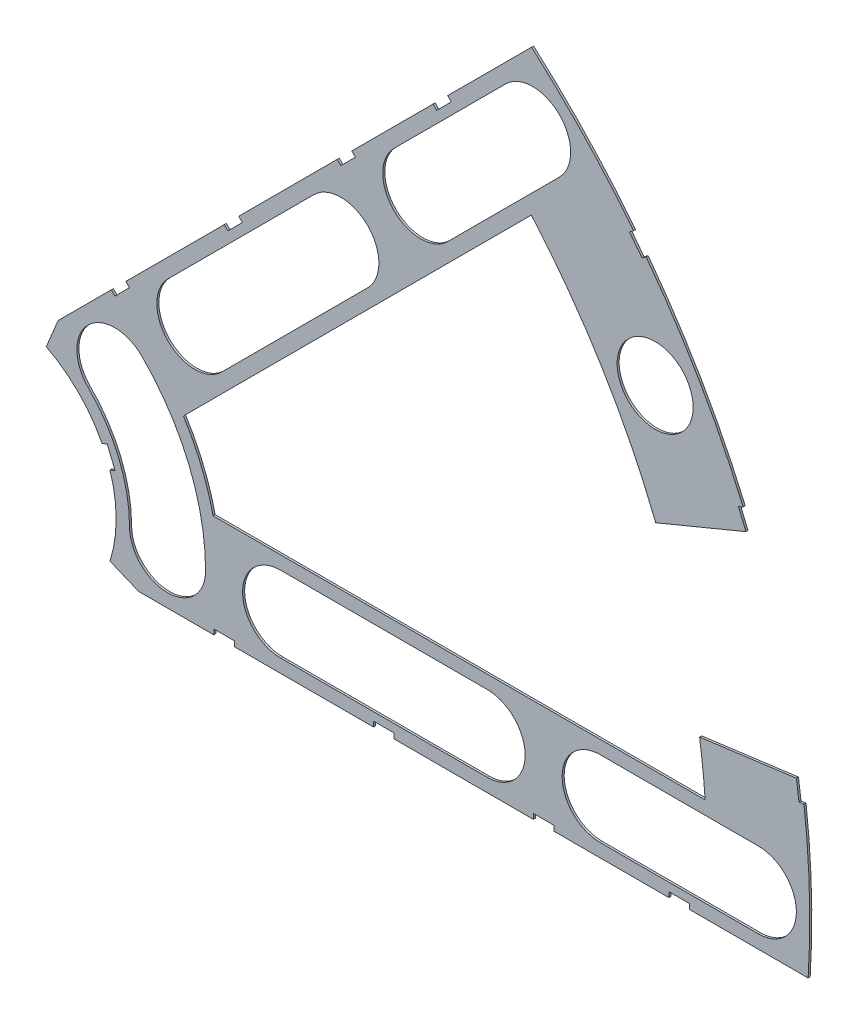
SolidWorks part; units mm, degrees
material "PTFE (general)"
ref_plane "Front Plane" through (0, 0, 0) normal (0, 0, 1) x (1, 0, 0)
ref_plane "Top Plane" through (0, 0, 0) normal (0, 1, 0) x (1, 0, 0)
ref_plane "Right Plane" through (0, 0, 0) normal (1, 0, 0) x (0, 0, -1)
sketch "Sketch1" plane through (0, 0, 0) normal (0, 0, 1) x (1, 0, 0)
  line L0 (0, 0) -> (320.3893, 0) construction
  line L1 (0, 0) -> (155.5285, 155.5285) construction
  line L2 (67.2115, 76.1917) -> (8.6967, 17.6769)
  line L3 (8.6967, 17.6769) -> (7.229, 14.1336)
  line L4 (101.4014, -6.35) -> (18.6489, -6.35)
  line L5 (15.1056, -4.8823) -> (18.6489, -6.35)
  line L6 (88.6729, 6.35) -> (27.8605, 6.35)
  line L9 (67.1914, 58.2111) -> (24.1905, 15.2102)
  line L10 (0, 0) -> (40.4486, 97.6516) construction
  line L11 (0, 0) -> (123.4567, -51.1374) construction
  line L18 (8.6967, 17.6769) -> (13.294, 8.6183) construction
  line L19 (18.6489, -6.35) -> (15.4943, 3.3063) construction
  line L20 (27.8605, 6.35) -> (27.7442, 6.7059) construction
  line L21 (24.1905, 15.2102) -> (24.3599, 14.8764) construction
  arc A0 (7.229, 14.1336) -> (15.1056, -4.8823) centre (0, 0) cw
  arc A1 (67.2115, 76.1917) -> (101.4014, -6.35) centre (0, 0) cw
  arc A2 (24.1905, 15.2102) -> (27.8605, 6.35) centre (0, 0) cw
  arc A3 (67.1914, 58.2111) -> (88.6729, 6.35) centre (0, 0) cw
  arc A8 (13.294, 8.6183) -> (15.4943, 3.3063) centre (0, 0) cw construction
  arc A9 (24.3599, 14.8764) -> (27.7442, 6.7059) centre (0, 0) cw construction
  dimension "D1" = 45
  dimension "D3" = 6.35
  dimension "D4" = 15.875
  dimension "D7" = 22.5
  dimension "D8" = 101.6
  dimension "D11" = 12.7
  dimension "D12" = 12.7
  dimension "D2" = 6.35
  dimension "D5" = 67.5
  dimension "D9" = 1.27
  dimension "D10" = 1.27
  dimension "D6" = 12.7
extrude "Boss-Extrude1" add sketch "Sketch1" along normal blind 0.254
sketch "Sketch2" plane through (0, 0, 0.254) normal (0, 0, 1) x (1, 0, 0)
  line L0 (0, 0) -> (101.6, 0) construction
  line L1 (0, 0) -> (71.842, 71.842) construction
  line L3 (0, 0) -> (22.225, 0) construction
  line L4 (0, 0) -> (15.7154, 15.7154) construction
  line L5 (0, 0) -> (95.25, 0) construction
  line L6 (0, 0) -> (92.0044, 24.6525) construction
  arc A0 (101.4014, -6.35) -> (67.2115, 76.1917) centre (0, 0) ccw construction
  circle A1 centre (22.225, 0) radius 4.699
  arc A2 (15.1056, -4.8823) -> (7.229, 14.1336) centre (0, 0) ccw construction
  circle A3 centre (36.195, 0) radius 4.699
  circle A4 centre (61.722, 0) radius 4.699
  circle A5 centre (75.692, 0) radius 4.699
  circle A6 centre (95.25, 0) radius 4.699
  circle A7 centre (15.7154, 15.7154) radius 4.699
  circle A8 centre (25.5937, 25.5937) radius 4.699
  circle A9 centre (43.644, 43.644) radius 4.699
  circle A10 centre (53.5223, 53.5223) radius 4.699
  circle A11 centre (92.0044, 24.6525) radius 4.699
  circle A12 centre (82.4889, 47.625) radius 4.699
  circle A13 centre (67.3519, 67.3519) radius 4.699
  dimension "D3" = 9.398
  dimension "D1" = 45
  dimension "D2" = 6.35
  dimension "D4" = 6.35
  dimension "D5" = 13.97
  dimension "D7" = 13.97
  dimension "D8" = 19.558
  dimension "D9" = 45
  dimension "D10" = 15
  dimension "D11" = 25.527
  dimension "D6" = 2
extrude "Cut-Extrude1" cut sketch "Sketch2" against normal through all
sketch "Sketch3" plane through (0, 0, 0.254) normal (0, 0, 1) x (1, 0, 0)
  line L0 (15.2664, 24.2467) -> (17.0625, 26.0427)
  line L1 (15.2664, 24.2467) -> (15.7154, 23.7977)
  line L2 (17.0625, 26.0427) -> (17.5115, 25.5937)
  line L3 (15.7154, 23.7977) -> (17.5115, 25.5937)
  line L4 (67.2115, 76.1917) -> (8.6967, 17.6769) construction
  line L5 (44.9911, 53.9713) -> (43.195, 52.1753)
  line L6 (44.9911, 53.9713) -> (45.4401, 53.5223)
  line L7 (43.195, 52.1753) -> (43.644, 51.7263)
  line L8 (45.4401, 53.5223) -> (43.644, 51.7263)
  line L9 (27.94, -6.35) -> (30.48, -6.35)
  line L10 (27.94, -6.35) -> (27.94, -5.715)
  line L11 (30.48, -6.35) -> (30.48, -5.715)
  line L12 (27.94, -5.715) -> (30.48, -5.715)
  line L13 (18.6489, -6.35) -> (101.4014, -6.35) construction
  line L14 (67.437, -6.35) -> (69.977, -6.35)
  line L15 (67.437, -6.35) -> (67.437, -5.715)
  line L16 (69.977, -6.35) -> (69.977, -5.715)
  line L17 (67.437, -5.715) -> (69.977, -5.715)
  line L18 (29.2307, 38.211) -> (31.0268, 40.007)
  line L19 (29.2307, 38.211) -> (29.6797, 37.762)
  line L20 (31.0268, 40.007) -> (31.4758, 39.558)
  line L21 (29.6797, 37.762) -> (31.4758, 39.558)
  line L22 (56.845, 65.8253) -> (55.049, 64.0292)
  line L23 (56.845, 65.8253) -> (57.294, 65.3763)
  line L24 (55.049, 64.0292) -> (55.498, 63.5802)
  line L25 (57.294, 65.3763) -> (55.498, 63.5802)
  line L26 (47.6885, -6.35) -> (50.2285, -6.35)
  line L27 (47.6885, -6.35) -> (47.6885, -5.715)
  line L28 (50.2285, -6.35) -> (50.2285, -5.715)
  line L29 (47.6885, -5.715) -> (50.2285, -5.715)
  line L30 (84.201, -6.35) -> (86.741, -6.35)
  line L31 (84.201, -6.35) -> (84.201, -5.715)
  line L32 (86.741, -6.35) -> (86.741, -5.715)
  line L33 (84.201, -5.715) -> (86.741, -5.715)
  line L34 (0, 0) -> (100.7308, 13.2615) construction
  line L35 (0, 0) -> (93.8662, 38.8806) construction
  line L36 (0, 0) -> (80.6047, 61.8502) construction
  line L37 (0, 0) -> (101.6, 0) construction
  line L38 (99.9355, 14.4377) -> (100.267, 11.9194)
  line L39 (99.9355, 14.4377) -> (101.1946, 14.6035)
  line L40 (100.267, 11.9194) -> (101.5261, 12.0852)
  line L41 (101.1946, 14.6035) -> (101.5261, 12.0852)
  line L42 (99.9355, 14.4377) -> (101.5261, 12.0852) construction
  line L43 (100.267, 11.9194) -> (101.1946, 14.6035) construction
  line L44 (93.7655, 37.4643) -> (94.9388, 37.9503)
  line L45 (93.7655, 37.4643) -> (92.7935, 39.811)
  line L46 (94.9388, 37.9503) -> (93.9668, 40.297)
  line L47 (92.7935, 39.811) -> (93.9668, 40.297)
  line L48 (93.7655, 37.4643) -> (93.9668, 40.297) construction
  line L49 (94.9388, 37.9503) -> (92.7935, 39.811) construction
  line L50 (79.3278, 62.4712) -> (80.874, 60.456)
  line L51 (79.3278, 62.4712) -> (80.3354, 63.2443)
  line L52 (80.874, 60.456) -> (81.8816, 61.2292)
  line L53 (80.3354, 63.2443) -> (81.8816, 61.2292)
  line L54 (79.3278, 62.4712) -> (81.8816, 61.2292) construction
  line L55 (80.874, 60.456) -> (80.3354, 63.2443) construction
  line L56 (13.5939, 7.0054) -> (14.5659, 4.6588)
  line L57 (13.5939, 7.0054) -> (14.7672, 7.4914)
  line L58 (14.5659, 4.6588) -> (15.7393, 5.1448)
  line L59 (14.7672, 7.4914) -> (15.7393, 5.1448)
  line L60 (13.5939, 7.0054) -> (15.7393, 5.1448) construction
  line L61 (14.5659, 4.6588) -> (14.7672, 7.4914) construction
  circle A0 centre (15.7154, 15.7154) radius 4.699 construction
  circle A1 centre (43.644, 43.644) radius 4.699 construction
  circle A2 centre (22.225, 0) radius 4.699 construction
  circle A3 centre (61.722, 0) radius 4.699 construction
  arc A4 (101.4014, -6.35) -> (67.2115, 76.1917) centre (0, 0) ccw construction
  arc A9 (15.1056, -4.8823) -> (7.229, 14.1336) centre (0, 0) ccw construction
  circle A10 centre (36.195, 0) radius 4.699 construction
  circle A11 centre (75.692, 0) radius 4.699 construction
  circle A12 centre (25.5937, 25.5937) radius 4.699 construction
  circle A13 centre (53.5223, 53.5223) radius 4.699 construction
  point P75 (14.6666, 6.0751)
  dimension "D2" = 5.715
  dimension "D3" = 2.54
  dimension "D6" = 5.715
  dimension "D8" = 0.635
  dimension "D9" = 5.715
  dimension "D12" = 5.715
  dimension "D4" = 7.5
  dimension "D5" = 22.5
  dimension "D7" = 37.5
  dimension "D10" = 90
  dimension "D11" = 1.27
  dimension "D14" = 0.635
  dimension "D15" = 90
  dimension "D18" = 0.635
  dimension "D19" = 90
  dimension "D22" = 0.635
  dimension "D20" = 1.27
  dimension "D17" = 0.635
  dimension "D13" = 11.4935
  dimension "D16" = 8.509
  dimension "D21" = 11.4935
  dimension "D23" = 8.509
extrude "Cut-Extrude2" cut sketch "Sketch3" against normal through all
sketch "Sketch5" plane through (0, 0, 0.254) normal (0, 0, 1) x (1, 0, 0)
  line L0 (0, 0) -> (99.623, 41.2652) construction
  line L1 (0, 0) -> (107.1415, 14.1054) construction
  line L2 (86.741, -6.35) -> (101.4014, -6.35) construction
  line L3 (100.267, 11.9194) -> (100.8887, 12.0013) construction
  line L4 (69.977, -6.35) -> (84.201, -6.35) construction
  line L5 (81.3901, 32.4757) -> (95.471, 38.3082)
  line L6 (93.3728, 40.0509) -> (92.7935, 39.811) construction
  line L8 (86.7237, 12.5703) -> (101.8344, 14.5596)
  arc A0 (86.7237, 12.5703) -> (81.3901, 32.4757) centre (0, 0) ccw
  arc A1 (95.471, 38.3082) -> (101.8344, 14.5596) centre (0, 0) cw
  arc A2 (88.6729, 6.35) -> (67.1914, 58.2111) centre (0, 0) ccw construction
  arc A3 (100.5572, 14.5196) -> (94.3448, 37.7043) centre (0, 0) ccw construction
  dimension "D3" = 1.27
  dimension "D4" = 1.27
  dimension "D1" = 7.5
  dimension "D2" = 22.5
  dimension "D5" = 2.413
  dimension "D6" = 2.413
sketch "Sketch6" plane through (0, 0, 0.254) normal (0, 0, 1) x (1, 0, 0)
  line L0 (0, 0) -> (101.6, 0) construction
  line L1 (0, 0) -> (71.842, 71.842) construction
  line L2 (0, 0) -> (87.9882, 50.8) construction
  line L3 (0, 0) -> (98.1381, 26.296) construction
  line L4 (25.5937, 25.5937) -> (43.644, 43.644) construction
  line L5 (22.271, 28.9164) -> (40.3213, 46.9667)
  line L6 (28.9164, 22.271) -> (46.9667, 40.3213)
  line L7 (53.5223, 53.5223) -> (67.3519, 67.3519) construction
  line L8 (50.1996, 56.845) -> (64.0292, 70.6746)
  line L9 (56.845, 50.1996) -> (70.6746, 64.0292)
  line L10 (61.722, 0) -> (36.195, 0) construction
  line L11 (61.722, -4.699) -> (36.195, -4.699)
  line L12 (61.722, 4.699) -> (36.195, 4.699)
  line L13 (95.25, 0) -> (75.692, 0) construction
  line L14 (95.25, -4.699) -> (75.692, -4.699)
  line L15 (95.25, 4.699) -> (75.692, 4.699)
  arc A0 (79.8253, 62.8529) -> (67.2115, 76.1917) centre (0, 0) ccw construction
  arc A1 (15.7154, 15.7154) -> (22.225, 0) centre (0, 0) cw construction
  arc A2 (26.924, 0) -> (19.0381, 19.0381) centre (0, 0) ccw
  arc A3 (17.526, 0) -> (12.3928, 12.3928) centre (0, 0) ccw
  arc A4 (17.526, 0) -> (26.924, 0) centre (22.225, 0) ccw
  arc A5 (101.4014, -6.35) -> (100.8887, 12.0013) centre (0, 0) ccw construction
  arc A6 (19.0381, 19.0381) -> (12.3928, 12.3928) centre (15.7154, 15.7154) ccw
  arc A7 (93.3728, 40.0509) -> (81.3715, 60.8378) centre (0, 0) ccw construction
  arc A8 (100.5572, 14.5196) -> (94.3448, 37.7043) centre (0, 0) ccw construction
  circle A9 centre (43.644, 43.644) radius 4.699 construction
  circle A10 centre (67.3519, 67.3519) radius 4.699 construction
  arc A14 (22.271, 28.9164) -> (28.9164, 22.271) centre (25.5937, 25.5937) ccw
  arc A15 (46.9667, 40.3213) -> (40.3213, 46.9667) centre (43.644, 43.644) ccw
  arc A16 (50.1996, 56.845) -> (56.845, 50.1996) centre (53.5223, 53.5223) ccw
  arc A17 (70.6746, 64.0292) -> (64.0292, 70.6746) centre (67.3519, 67.3519) ccw
  arc A18 (61.722, -4.699) -> (61.722, 4.699) centre (61.722, 0) ccw
  arc A19 (36.195, 4.699) -> (36.195, -4.699) centre (36.195, 0) ccw
  arc A20 (95.25, -4.699) -> (95.25, 4.699) centre (95.25, 0) ccw
  arc A21 (75.692, 4.699) -> (75.692, -4.699) centre (75.692, 0) ccw
  point P8 (20.5332, 8.5051)
  point P43 (34.6189, 34.6189)
  point P48 (60.4371, 60.4371)
  point P59 (48.9585, 0)
  point P70 (85.471, 0)
  dimension "D5" = 9.398
  dimension "D1" = 45
  dimension "D3" = 9.398
  dimension "D4" = 9.398
extrude "Cut-Extrude4" cut sketch "Sketch6" against normal through all
extrude "Cut-Extrude5" cut sketch "Sketch5" against normal through all
equation "\"cSep\"= 1.005"
equation "\"D11@Sketch2\"=\"cSep\""
equation "\"cSep2\"= \"D8@Sketch2\""
equation "\"D13@Sketch3\"=\"cSep\"/2-.05"
equation "\"D16@Sketch3\"=\"cSep2\"/2-.05"
equation "\"D21@Sketch3\"=\"cSep\"/2-.05"
equation "\"D23@Sketch3\"=\"cSep2\"/2-.05"
